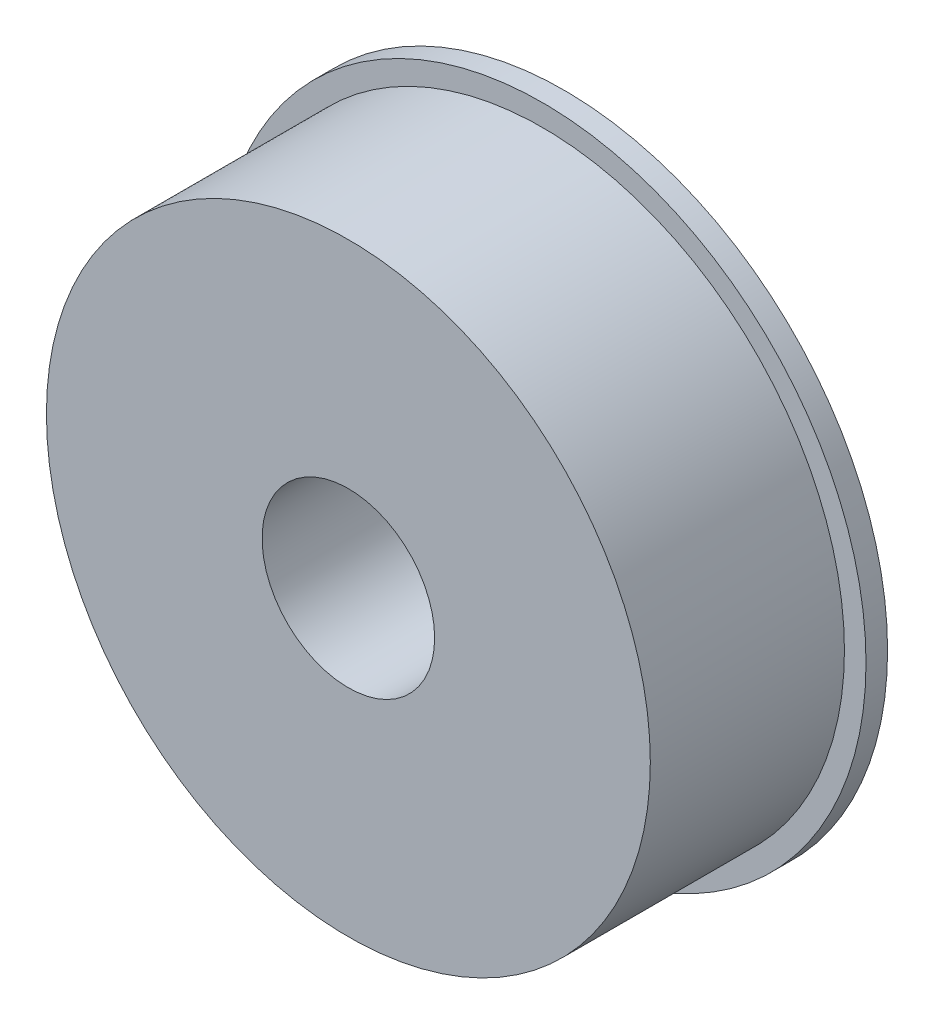
SolidWorks part; units mm, degrees
ref_plane "Front Plane" through (0, 0, 0) normal (0, 0, 1) x (1, 0, 0)
ref_plane "Top Plane" through (0, 0, 0) normal (0, 1, 0) x (1, 0, 0)
ref_plane "Right Plane" through (0, 0, 0) normal (1, 0, 0) x (0, 0, -1)
sketch "Sketch1" plane through (0, 0, 0) normal (0, 0, 1) x (1, 0, 0)
  circle A0 centre (0, 0) radius 25
  circle A1 centre (0, 0) radius 87.5
  dimension "D1" = 50
  dimension "D2" = 175
extrude "Boss-Extrude1" add sketch "Sketch1" along normal blind 62.5
sketch "Sketch2" plane through (0, 0, 0) normal (0, 0, 1) x (1, 0, 0)
  circle A0 centre (0, 0) radius 93.75
  dimension "D1" = 187.5
extrude "Boss-Extrude3" add sketch "Sketch2" along normal blind 6.25
